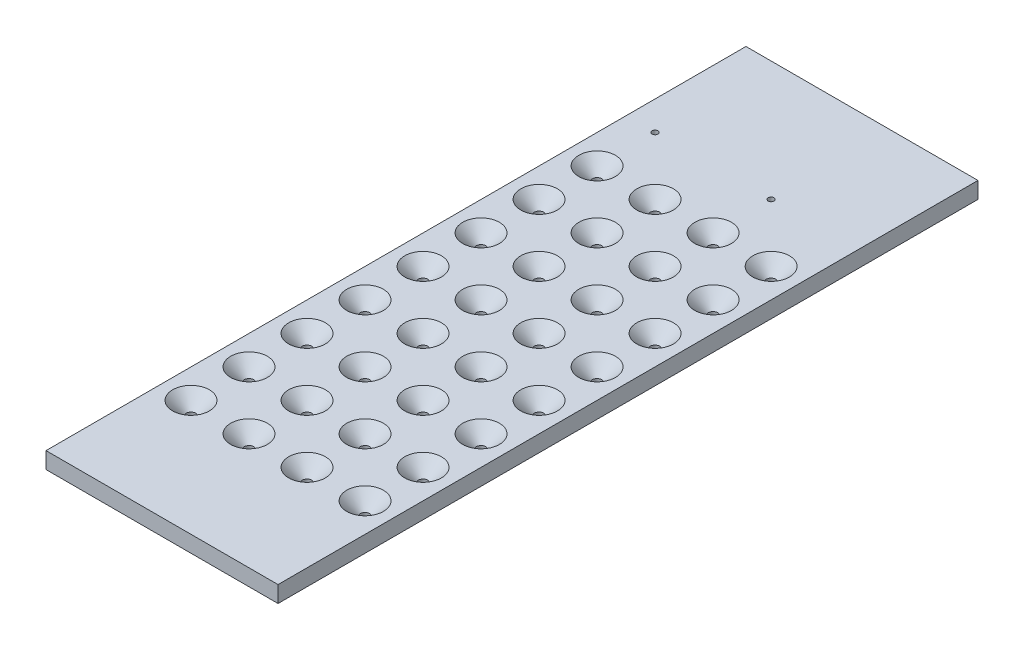
SolidWorks part; units mm, degrees
material "Chêne"
ref_plane "Plan de face" through (0, 0, 0) normal (0, 0, 1) x (1, 0, 0)
ref_plane "Plan de dessus" through (0, 0, 0) normal (0, 1, 0) x (1, 0, 0)
ref_plane "Plan de droite" through (0, 0, 0) normal (1, 0, 0) x (0, 0, -1)
sketch "Esquisse1" plane through (0, 0, 0) normal (0, 1, 0) x (1, 0, 0)
  line L1 (-60, -181) -> (60, -181)
  line L2 (-60, -181) -> (-60, 181)
  line L3 (-60, 181) -> (60, 181)
  line L4 (60, -181) -> (60, 181)
  line L5 (-60, -181) -> (60, 181) construction
  line L6 (-60, 181) -> (60, -181) construction
  point P0 (0, 0)
  dimension "D1" = 120
  dimension "D2" = 362
extrude "Boss.-Extru.1" add sketch "Esquisse1" against normal blind 8.5
sketch "Esquisse2" plane through (0, 0, 0) normal (0, 1, 0) x (1, 0, 0)
  line L0 (60, 181) -> (-60, 181) construction
  line L1 (-60, 181) -> (-60, -181) construction
  line L2 (-45, 89) -> (-15, 89) construction
  line L3 (-45, 89) -> (-45, 59) construction
  circle A0 centre (-45, 89) radius 2.5
  circle A32 centre (-45, 119) radius 1.5
  circle A33 centre (15, 119) radius 1.5
  circle A34 centre (-15, 89) radius 2.5
  circle A35 centre (15, 89) radius 2.5
  circle A36 centre (45, 89) radius 2.5
  circle A37 centre (-15, 59) radius 2.5
  circle A38 centre (15, 59) radius 2.5
  circle A39 centre (45, 59) radius 2.5
  circle A40 centre (-15, 29) radius 2.5
  circle A41 centre (15, 29) radius 2.5
  circle A42 centre (45, 29) radius 2.5
  circle A43 centre (-15, -1) radius 2.5
  circle A44 centre (15, -1) radius 2.5
  circle A45 centre (45, -1) radius 2.5
  circle A46 centre (-15, -31) radius 2.5
  circle A47 centre (15, -31) radius 2.5
  circle A48 centre (45, -31) radius 2.5
  circle A49 centre (-15, -61) radius 2.5
  circle A50 centre (15, -61) radius 2.5
  circle A51 centre (45, -61) radius 2.5
  circle A52 centre (-15, -91) radius 2.5
  circle A53 centre (15, -91) radius 2.5
  circle A54 centre (45, -91) radius 2.5
  circle A55 centre (-15, -121) radius 2.5
  circle A56 centre (15, -121) radius 2.5
  circle A57 centre (45, -121) radius 2.5
  circle A58 centre (-45, 59) radius 2.5
  circle A59 centre (-45, 29) radius 2.5
  circle A60 centre (-45, -1) radius 2.5
  circle A61 centre (-45, -31) radius 2.5
  circle A62 centre (-45, -61) radius 2.5
  circle A63 centre (-45, -91) radius 2.5
  circle A64 centre (-45, -121) radius 2.5
  dimension "D1" = 5
  dimension "D6" = 3
  dimension "D7" = 3
  dimension "D2" = 92
  dimension "D3" = 15
  dimension "D8" = 30
  dimension "D9" = 30
  dimension "D10" = 30
  dimension "D4" = 4
  dimension "D5" = 8
extrude "Enlèv. mat.-Extru.1" cut sketch "Esquisse2" against normal through all
chamfer "Chanfrein1" distance 7 angle 45 32 edges at (-45, 0, -86.5) (-45, 0, -56.5) (-15, 0, -56.5) (-15, 0, -86.5) (15, 0, -86.5) (45, 0, -86.5) (15, 0, -56.5) (45, 0, -56.5) (-15, 0, -26.5) (15, 0, -26.5) (45, 0, -26.5) (-15, 0, 3.5) (15, 0, 3.5) (45, 0, 3.5) (-15, 0, 33.5) (15, 0, 33.5) (45, 0, 33.5) (-15, 0, 63.5) (15, 0, 63.5) (45, 0, 63.5) (-15, 0, 93.5) (15, 0, 93.5) (45, 0, 93.5) (-15, 0, 123.5) (15, 0, 123.5) (45, 0, 123.5) (-45, 0, -26.5) (-45, 0, 3.5) (-45, 0, 33.5) (-45, 0, 63.5) (-45, 0, 93.5) (-45, 0, 123.5)
